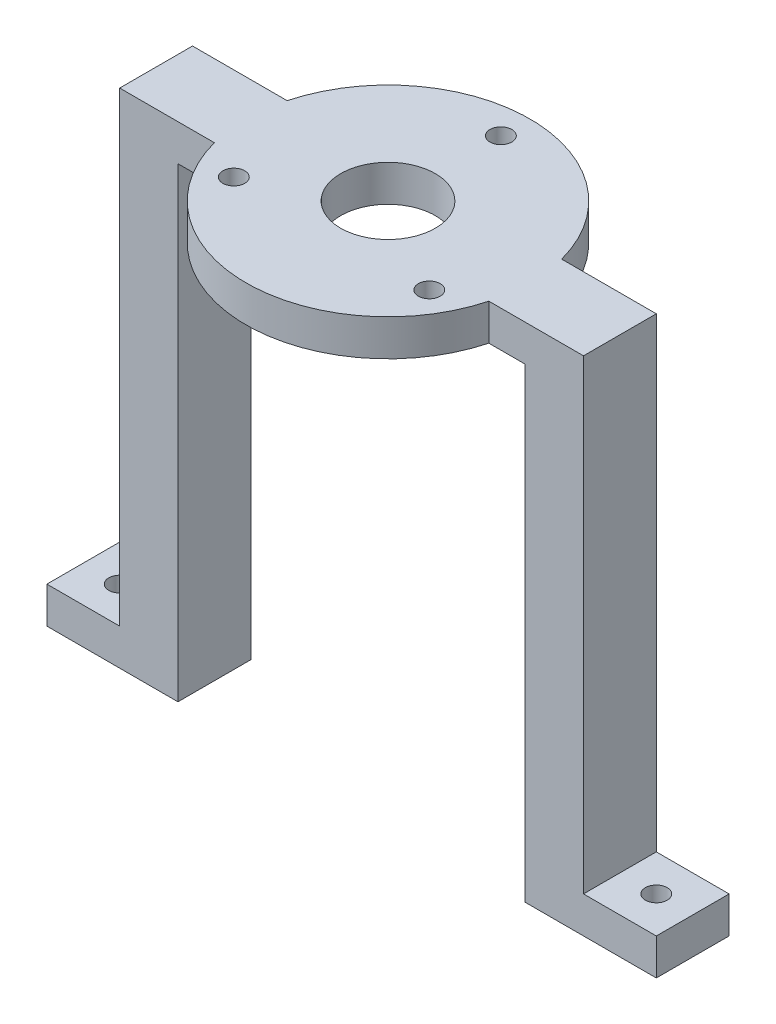
SolidWorks part; units mm, degrees
ref_plane "Front Plane" through (0, 0, 0) normal (0, 0, 1) x (1, 0, 0)
ref_plane "Top Plane" through (0, 0, 0) normal (0, 1, 0) x (1, 0, 0)
ref_plane "Right Plane" through (0, 0, 0) normal (1, 0, 0) x (0, 0, -1)
sketch "Sketch1" plane through (0, 0, 0) normal (0, 1, 0) x (1, 0, 0)
  line L0 (48.7044, 0) -> (-48.7044, 0) construction
  line L1 (0, -25.0907) -> (0, 25.0907) construction
  line L2 (-31.8481, -5) -> (-18.8481, -5)
  line L3 (-31.8481, -5) -> (-31.8481, 5)
  line L4 (-31.8481, 5) -> (-18.8481, 5)
  line L6 (-31.8481, -5) -> (-18.8481, 5) construction
  line L7 (-31.8481, 5) -> (-18.8481, -5) construction
  line L8 (31.8481, -5) -> (18.8481, -5)
  line L9 (31.8481, -5) -> (31.8481, 5)
  line L10 (31.8481, 5) -> (18.8481, 5)
  arc A0 (-18.8481, -5) -> (18.8481, -5) centre (0, 0) ccw
  circle A1 centre (0, 0) radius 6.5
  arc A2 (18.8481, 5) -> (-18.8481, 5) centre (0, 0) ccw
  point P6 (0, 0)
  point P7 (-25.3481, 0)
  point P14 (0, 0)
  dimension "D1" = 39
  dimension "D2" = 13
  dimension "D3" = 13
  dimension "D4" = 10
extrude "Boss-Extrude1" add sketch "Sketch1" along normal blind 5
sketch "Sketch2" plane through (0, 0, 0) normal (0, -1, 0) x (1, 0, 0)
  line L0 (-18.8481, -5) -> (-31.8481, -5) construction
  line L1 (-31.8481, 5) -> (-23.8481, 5)
  line L2 (-31.8481, 5) -> (-31.8481, -5)
  line L3 (-31.8481, -5) -> (-23.8481, -5)
  line L4 (-23.8481, 5) -> (-23.8481, -5)
  line L5 (0, -35.7776) -> (0, 35.7776) construction
  line L6 (31.8481, -5) -> (23.8481, -5)
  line L7 (23.8481, 5) -> (23.8481, -5)
  line L8 (31.8481, 5) -> (23.8481, 5)
  line L9 (31.8481, 5) -> (31.8481, -5)
  point P11 (0, 0)
  dimension "D1" = 8
extrude "Boss-Extrude2" add sketch "Sketch2" along normal blind 64
sketch "Sketch5" plane through (-31.8481, 0, 0) normal (-1, 0, 0) x (0, 0, 1)
  line L0 (-5, 5) -> (-5, -64) construction
  line L1 (-5, -59) -> (5, -59)
  line L2 (-5, -59) -> (-5, -64)
  line L3 (-5, -64) -> (5, -64)
  line L4 (5, -59) -> (5, -64)
  dimension "D1" = 5
extrude "Boss-Extrude3" add sketch "Sketch5" along normal blind 10
sketch "Sketch6" plane through (31.8481, 0, 0) normal (1, 0, 0) x (0, 0, -1)
  line L0 (5, 5) -> (5, -64) construction
  line L1 (-5, -64) -> (5, -64)
  line L2 (-5, -64) -> (-5, -59)
  line L3 (-5, -59) -> (5, -59)
  line L4 (5, -64) -> (5, -59)
  dimension "D1" = 5
extrude "Boss-Extrude4" add sketch "Sketch6" along normal blind 10
hole_wizard "Ø3.0mm Dowel Hole1" positions "Sketch9" profile "Sketch8" hole size "Ø3.0" standard "ISO"
sketch "Sketch9" plane through (0, -59, 0) normal (0, 1, 0) x (1, 0, 0)
  line L0 (41.8481, 5) -> (41.8481, -5) construction
  line L1 (-41.8481, -5) -> (-41.8481, 5) construction
  point P0 (36.8481, 0)
  point P5 (-36.8481, 0)
  dimension "D1" = 5
  dimension "D2" = 5
sketch "Sketch8" plane through (36.8481, -59, 0) normal (1, 0, 0) x (0, 0, 1)
  line L0 (0, 0) -> (0, 23.9013)
  line L1 (0, 23.9013) -> (1.5, 23)
  line L2 (1.5, 23) -> (1.5, 0)
  line L5 (1.5, 0) -> (0, 0)
  line L10 (0, 23.9013) -> (-1.5, 23) construction
  line L11 (0, -6.35) -> (0, 107.95) construction
  dimension "Hole Dia." = 3
  dimension "Hole Depth" = 23
  dimension "Drill Angle" = 118
hole_wizard "Ø3.0mm Dowel Hole2" positions "Sketch11" profile "Sketch12" hole size "Ø3.0" standard "ISO" end condition through all
sketch "Sketch11" plane through (0, 5, 0) normal (0, 1, 0) x (1, 0, 0)
  point P0 (0, 15.5)
  point P9 (13.4234, -7.75)
  point P10 (-13.4234, -7.75)
  dimension "D1" = 15.5
  dimension "D2" = 3
sketch "Sketch12" plane through (0, 5, -15.5) normal (1, 0, 0) x (0, 0, 1)
  line L0 (0, 0) -> (0, 69)
  line L1 (0, 69) -> (1.5, 69)
  line L2 (1.5, 69) -> (1.5, 0)
  line L5 (1.5, 0) -> (0, 0)
  line L11 (0, -6.35) -> (0, 107.95) construction
  dimension "Thru Hole Dia." = 3
  dimension "Thru Hole Depth" = 69
